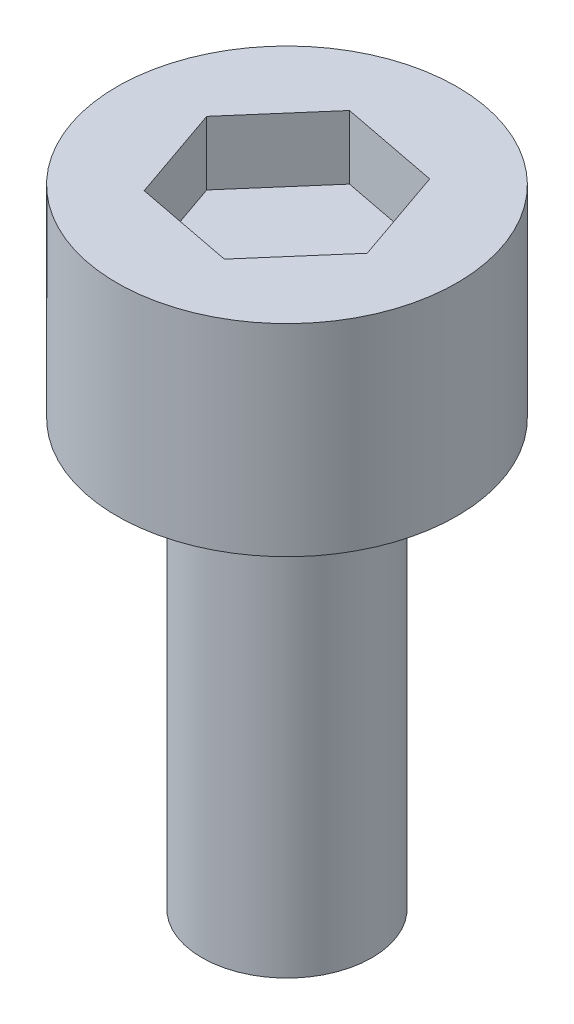
SolidWorks part; units mm, degrees
ref_plane "Front Plane" through (0, 0, 0) normal (0, 0, 1) x (1, 0, 0)
ref_plane "Top Plane" through (0, 0, 0) normal (0, 1, 0) x (1, 0, 0)
ref_plane "Right Plane" through (0, 0, 0) normal (1, 0, 0) x (0, 0, -1)
sketch "Sketch1" plane through (0, 0, 0) normal (0, 0, 1) x (1, 0, 0)
  line L0 (0, 0) -> (0, 36.502) construction
  line L1 (0, 0) -> (4, 0)
  line L2 (4, 0) -> (4, 20)
  line L3 (4, 20) -> (8, 20)
  line L4 (8, 20) -> (8, 29.5)
  line L5 (8, 29.5) -> (0, 29.5)
  line L6 (0, 0) -> (0, 29.5)
  dimension "D1" = 8
  dimension "D2" = 20
  dimension "D3" = 9.5
  dimension "D4" = 16
revolve "Revolve1" add sketch "Sketch1" angle 360 about L0
sketch "Sketch2" plane through (0, 29.5, 0) normal (0, 1, 0) x (1, 0, 0)
  line L1 (3.1191, 3.5989) -> (-1.5572, 4.5007)
  line L2 (-1.5572, 4.5007) -> (-4.6763, 0.9018)
  line L3 (-4.6763, 0.9018) -> (-3.1191, -3.5989)
  line L4 (-3.1191, -3.5989) -> (1.5572, -4.5007)
  line L5 (1.5572, -4.5007) -> (4.6763, -0.9018)
  line L6 (4.6763, -0.9018) -> (3.1191, 3.5989)
  circle A0 centre (0, 0) radius 4.1244 construction
extrude "Cut-Extrude1" cut sketch "Sketch2" against normal blind 3
